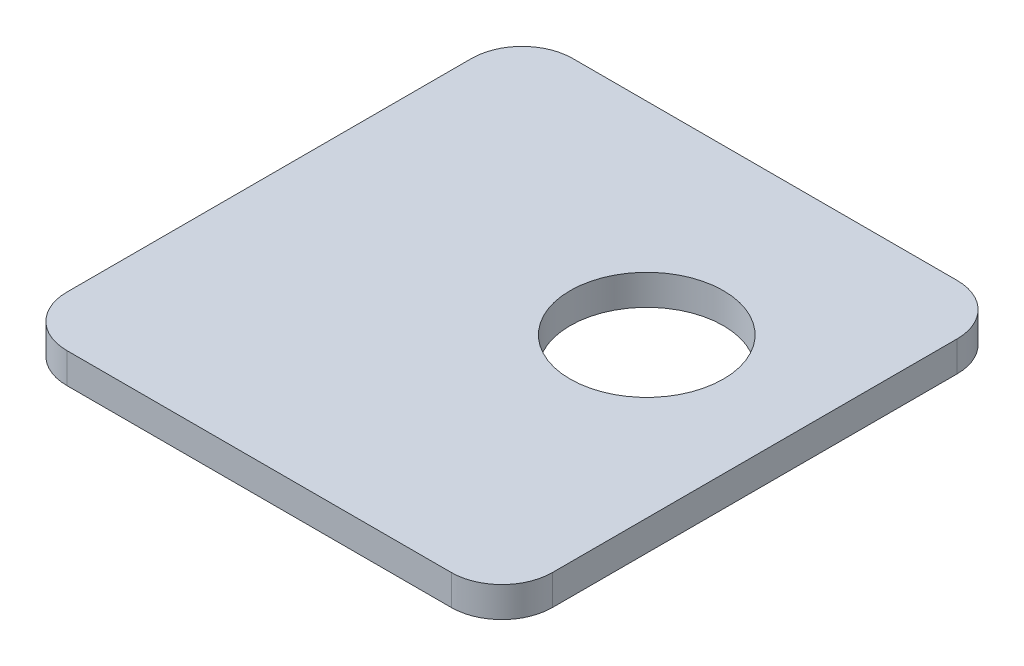
SolidWorks part; units mm, degrees
material "Acrylic (Medium-high impact)"
ref_plane "Front Plane" through (0, 0, 0) normal (0, 0, 1) x (1, 0, 0)
ref_plane "Top Plane" through (0, 0, 0) normal (0, 1, 0) x (1, 0, 0)
ref_plane "Right Plane" through (0, 0, 0) normal (1, 0, 0) x (0, 0, -1)
sketch "Sketch1" plane through (0, 0, 0) normal (0, 1, 0) x (1, 0, 0)
  line L1 (-19.4223, 29.2067) -> (18.5777, 29.2067)
  line L2 (-24.4223, 24.2067) -> (-24.4223, -15.7933)
  line L3 (-19.4223, -20.7933) -> (18.5777, -20.7933)
  line L4 (23.5777, 24.2067) -> (23.5777, -15.7933)
  arc A0 (-24.4223, 24.2067) -> (-19.4223, 29.2067) centre (-19.4223, 24.2067) cw
  arc A1 (-24.4223, -15.7933) -> (-19.4223, -20.7933) centre (-19.4223, -15.7933) ccw
  arc A2 (23.5777, -15.7933) -> (18.5777, -20.7933) centre (18.5777, -15.7933) cw
  arc A3 (23.5777, 24.2067) -> (18.5777, 29.2067) centre (18.5777, 24.2067) ccw
  circle A6 centre (7.8947, 9.2083) radius 7.575
  circle A7 centre (7.8947, 9.2083) radius 7.575
  point P6 (-24.4223, 29.2067)
  point P9 (-24.4223, -20.7933)
  point P14 (23.5777, 29.2067)
  dimension "D3" = 5
  dimension "D1" = 50
  dimension "D2" = 48
  dimension "D4" = 0.25
extrude "Boss-Extrude1" add sketch "Sketch1" along normal blind 3
